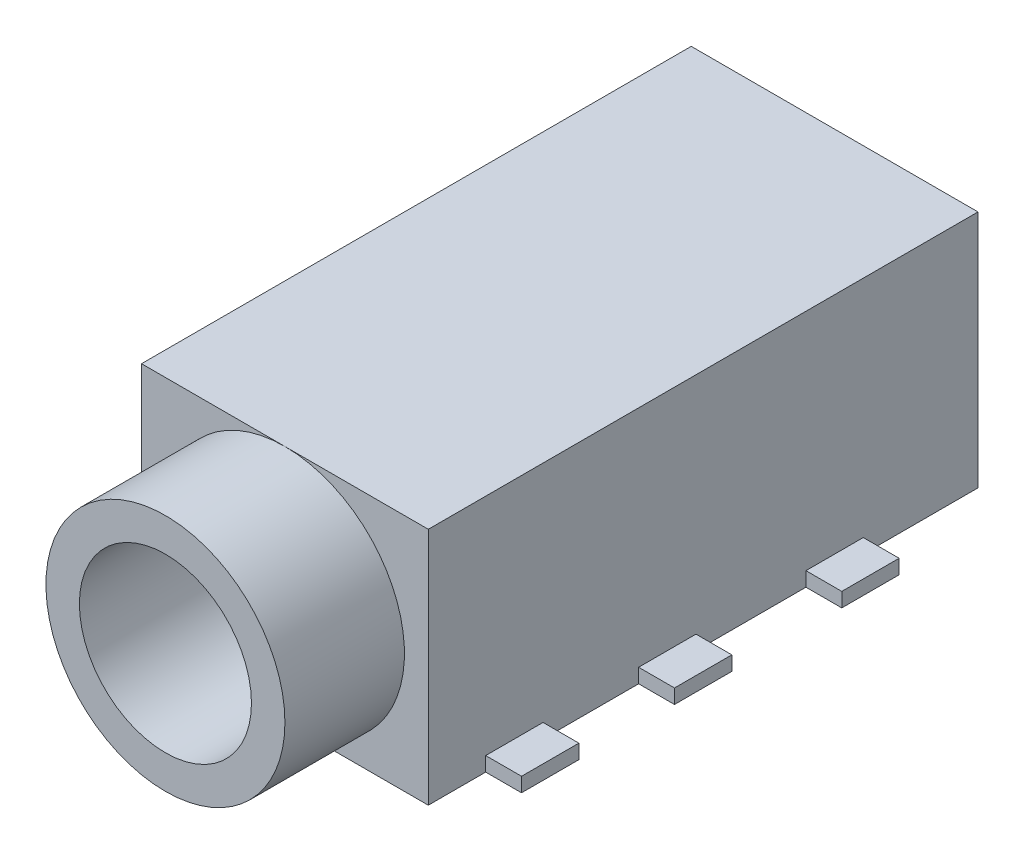
SolidWorks part; units mm, degrees
material "ABS"
ref_plane "Front Plane" through (0, 0, 0) normal (0, 0, 1) x (1, 0, 0)
ref_plane "Top Plane" through (0, 0, 0) normal (0, 1, 0) x (1, 0, 0)
ref_plane "Right Plane" through (0, 0, 0) normal (1, 0, 0) x (0, 0, -1)
sketch "Sketch1" plane through (0, 0, 0) normal (0, 0, 1) x (1, 0, 0)
  line L1 (-3, 2.5) -> (3, 2.5)
  line L2 (-3, 2.5) -> (-3, -2.5)
  line L3 (-3, -2.5) -> (3, -2.5)
  line L4 (3, 2.5) -> (3, -2.5)
  line L5 (-3, 2.5) -> (3, -2.5) construction
  line L6 (-3, -2.5) -> (3, 2.5) construction
  point P0 (0, 0)
  dimension "D1" = 5
  dimension "D2" = 6
extrude "Boss-Extrude1" add sketch "Sketch1" along normal blind 11.5
sketch "Sketch2" plane through (0, 0, 11.5) normal (0, 0, 1) x (1, 0, 0)
  circle A0 centre (0, 0) radius 2.5
  circle A1 centre (0, 0) radius 1.8
  dimension "D1" = 3.6
extrude "Boss-Extrude2" add sketch "Sketch2" along normal blind 2.5
sketch "Sketch3" plane through (0, 0, 11.5) normal (0, 0, 1) x (1, 0, 0)
  circle A0 centre (0, 0) radius 1.8
extrude "Cut-Extrude1" cut sketch "Sketch3" against normal blind 10
sketch "Sketch4" plane through (0, -2.5, 0) normal (0, -1, 0) x (1, 0, 0)
  line L0 (3, 11.5) -> (3, 0) construction
  line L1 (3, 10.3) -> (3.75, 10.3)
  line L2 (3, 10.3) -> (3, 9.1)
  line L3 (3, 9.1) -> (3.75, 9.1)
  line L4 (3.75, 10.3) -> (3.75, 9.1)
  line L5 (0, 11.5) -> (3, 11.5) construction
  line L6 (3, 7.1) -> (3.75, 7.1)
  line L7 (3, 5.9) -> (3.75, 5.9)
  line L8 (3.75, 7.1) -> (3.75, 5.9)
  line L9 (3, 7.1) -> (3, 5.9)
  line L10 (0, 14.8689) -> (0, -2.0842) construction
  line L11 (3, 3.6) -> (3.75, 3.6)
  line L12 (3, 3.6) -> (3, 2.4)
  line L13 (3, 2.4) -> (3.75, 2.4)
  line L14 (3.75, 3.6) -> (3.75, 2.4)
  line L15 (-3.75, 3.6) -> (-3.75, 2.4)
  line L16 (-3, 2.4) -> (-3.75, 2.4)
  line L17 (-3, 3.6) -> (-3, 2.4)
  line L18 (-3, 3.6) -> (-3.75, 3.6)
  line L19 (-3, 7.1) -> (-3, 5.9)
  line L20 (-3.75, 7.1) -> (-3.75, 5.9)
  line L21 (-3, 5.9) -> (-3.75, 5.9)
  line L22 (-3, 7.1) -> (-3.75, 7.1)
  line L23 (-3.75, 10.3) -> (-3.75, 9.1)
  line L24 (-3, 9.1) -> (-3.75, 9.1)
  line L25 (-3, 10.3) -> (-3, 9.1)
  line L26 (-3, 10.3) -> (-3.75, 10.3)
  line L27 (-3.75, 9.9189) -> (-3.75, 1.5525) construction
  line L28 (-3, 7.8181) -> (-3, 5.0664) construction
  line L29 (-3, 11.5) -> (-3, 0) construction
  point P10 (3.75, 6.5)
  point P14 (3.75, 9.7)
  point P19 (3.75, 3)
  dimension "D1" = 1.8
  dimension "D2" = 1.2
  dimension "D3" = 1.2
  dimension "D4" = 3.2
  dimension "D5" = 1.2
  dimension "D6" = 8.5
  dimension "D7" = 7.5
  dimension "D8" = 0
  dimension "D9" = 0
extrude "Boss-Extrude3" add sketch "Sketch4" against normal blind 0.3
sketch "Sketch5" plane through (0, -2.5, 0) normal (0, -1, 0) x (1, 0, 0)
  line L0 (-3, 11.5) -> (0, 11.5) construction
  circle A0 centre (0, 9) radius 0.75
  circle A1 centre (0, 3) radius 0.75
  dimension "D1" = 1.5
  dimension "D2" = 2.5
  dimension "D3" = 6
extrude "Boss-Extrude4" add sketch "Sketch5" along normal blind 0.6
equation "\"D5@Sketch4\"=\"D3@Sketch4\""
equation "\"D3@Sketch4\"=\"D2@Sketch4\""
